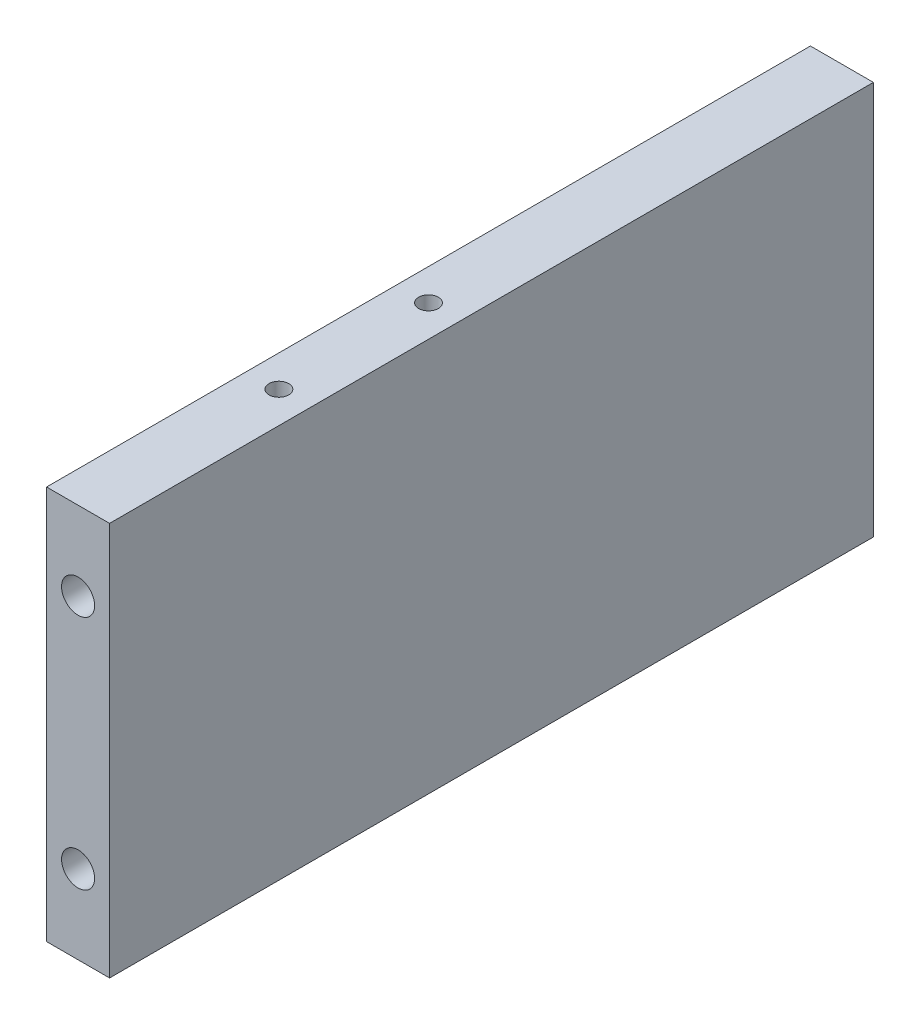
SolidWorks part; units mm, degrees
ref_plane "前视基准面" through (0, 0, 0) normal (0, 0, 1) x (1, 0, 0)
ref_plane "上视基准面" through (0, 0, 0) normal (0, 1, 0) x (1, 0, 0)
ref_plane "右视基准面" through (0, 0, 0) normal (1, 0, 0) x (0, 0, -1)
sketch "草图1" plane through (0, 0, 0) normal (0, 0, 1) x (1, 0, 0)
  line L1 (0, 0) -> (8, 0)
  line L2 (0, 0) -> (0, 50)
  line L3 (0, 50) -> (8, 50)
  line L4 (8, 0) -> (8, 50)
  dimension "D1" = 8
  dimension "D2" = 50
extrude "凸台-拉伸1" add sketch "草图1" along normal blind 97
hole_wizard "M5 螺纹孔2" positions "草图5" profile "草图6" tap size "M5" standard "ISO"
sketch "草图5" plane through (0, 0, 0) normal (0, 0, -1) x (-1, 0, 0)
  point P0 (-4, 40)
  point P3 (-4, 10)
sketch "草图6" plane through (4, 40, 0) normal (1, 0, 0) x (0, 1, 0)
  line L0 (0, 0) -> (0, 13.6618)
  line L1 (0, 13.6618) -> (2.1, 12.4)
  line L2 (2.1, 12.4) -> (2.1, 0)
  line L5 (2.1, 0) -> (0, 0)
  line L10 (0, 13.6618) -> (-2.1, 12.4) construction
  line L11 (0, -6.35) -> (0, 107.95) construction
  dimension "螺纹孔钻头直径" = 4.2
  dimension "螺纹孔钻头深度" = 12.4
  dimension "导头角度" = 118
cosmetic thread "孔螺蚊线3" parameters "D1"=10, "D2"=5
cosmetic thread "孔螺蚊线4" parameters "D1"=10, "D2"=5
ref_plane "基准面1" through (0, 0, 48.5) normal (0, 0, -1) x (-1, 0, 0)
mirror "镜向1" about plane through (0, 0, 48.5) normal (0, 0, -1) of "M5 螺纹孔2"
hole_wizard "M3 螺纹孔1" positions "草图7" profile "草图8" tap size "M3" standard "ISO"
sketch "草图7" plane through (0, 50, 0) normal (0, 1, 0) x (1, 0, 0)
  point P0 (4, -71.5)
  point P3 (4, -52.5)
sketch "草图8" plane through (4, 50, 71.5) normal (1, 0, 0) x (0, 0, 1)
  line L0 (0, 0) -> (0, 8.2511)
  line L1 (0, 8.2511) -> (1.25, 7.5)
  line L2 (1.25, 7.5) -> (1.25, 0)
  line L5 (1.25, 0) -> (0, 0)
  line L10 (0, 8.2511) -> (-1.25, 7.5) construction
  line L11 (0, -6.35) -> (0, 107.95) construction
  dimension "螺纹孔钻头直径" = 2.5
  dimension "螺纹孔钻头深度" = 7.5
  dimension "导头角度" = 118
cosmetic thread "孔螺蚊线5" parameters "D1"=6, "D2"=3
cosmetic thread "孔螺蚊线6" parameters "D1"=6, "D2"=3
